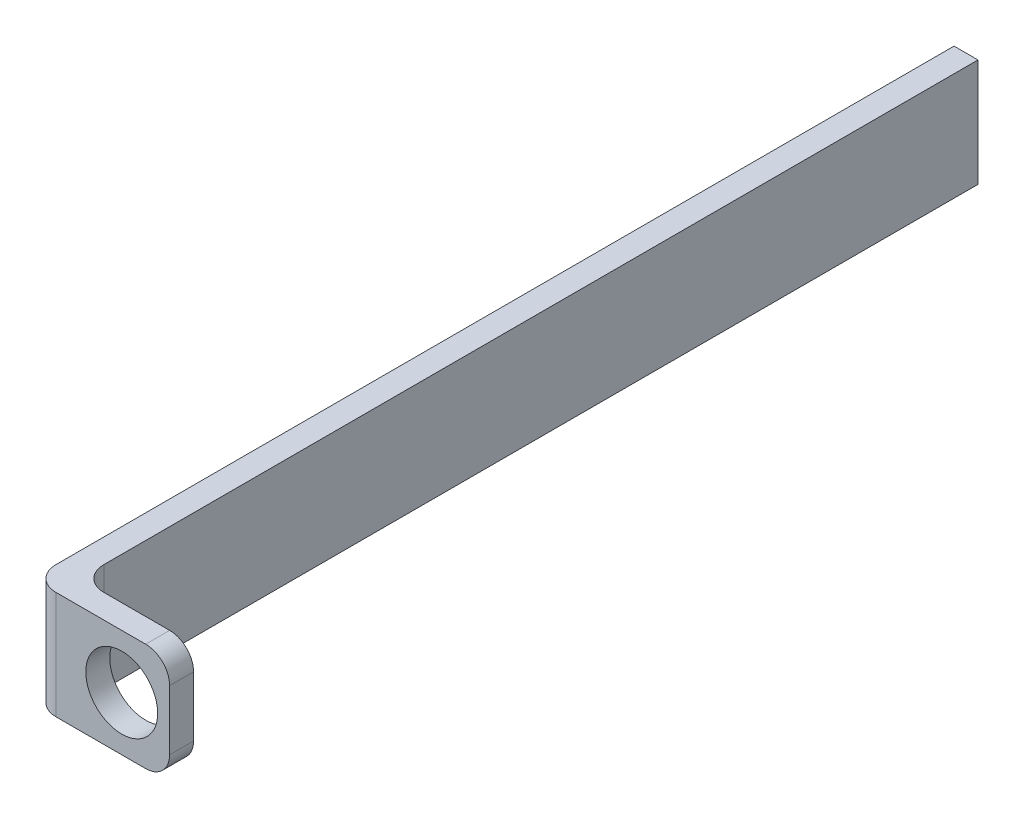
SolidWorks part; units mm, degrees
material "AISI 1020"
ref_plane "Front Plane" through (0, 0, 0) normal (0, 0, 1) x (1, 0, 0)
ref_plane "Top Plane" through (0, 0, 0) normal (0, 1, 0) x (1, 0, 0)
ref_plane "Right Plane" through (0, 0, 0) normal (1, 0, 0) x (0, 0, -1)
sketch "Sketch1" plane through (0, 0, 0) normal (0, 0, 1) x (1, 0, 0)
  line L0 (-1.3198, 0) -> (18.4624, 0) construction
  line L2 (0, 18.4636) -> (0, -11.7915) construction
  line L3 (0, 0) -> (23.3963, 0) construction
  line L4 (-7.5, 4.5) -> (2, 4.5)
  line L5 (-7.5, 4.5) -> (-7.5, -4.5)
  line L6 (-7.5, -4.5) -> (2, -4.5)
  line L7 (4, 2.5) -> (4, -2.5)
  circle A0 centre (0, 0) radius 3 construction
  circle A2 centre (0, 0) radius 3
  arc A4 (2, 4.5) -> (4, 2.5) centre (2, 2.5) cw
  arc A5 (2, -4.5) -> (4, -2.5) centre (2, -2.5) ccw
  point P8 (0, 0)
  point P9 (0, 0)
  point P12 (0, 0)
  dimension "D8" = 6
  dimension "D2" = 4.5
  dimension "D3" = 4
  dimension "D4" = 2
  dimension "D6" = 7.5
extrude "Boss-Extrude1" add sketch "Sketch1" along normal blind 2
sketch "Sketch2" plane through (0, 0, 0) normal (0, 0, -1) x (-1, 0, 0)
  line L0 (7.5, -4.5) -> (-2, -4.5) construction
  line L1 (7.5, 4.5) -> (5.5, 4.5)
  line L2 (7.5, 4.5) -> (7.5, -4.5)
  line L3 (7.5, -4.5) -> (5.5, -4.5)
  line L4 (5.5, 4.5) -> (5.5, -4.5)
  dimension "D1" = 2
extrude "Boss-Extrude2" add sketch "Sketch2" along normal blind 75
fillet "Fillet1" radius 2 2 edges at (-5.5, 0, 0) (-7.5, 0, 2)
